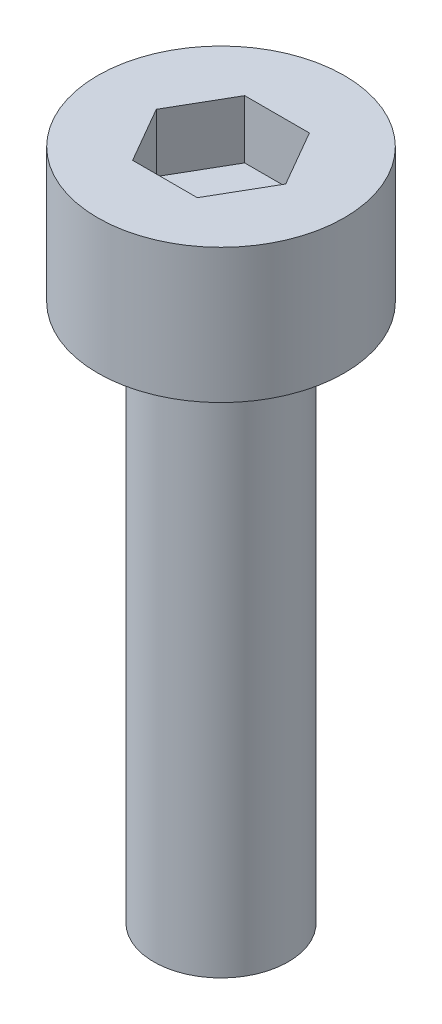
SolidWorks part; units mm, degrees
material "AISI 304"
ref_plane "前视基准面" through (0, 0, 0) normal (0, 0, 1) x (1, 0, 0)
ref_plane "上视基准面" through (0, 0, 0) normal (0, 1, 0) x (1, 0, 0)
ref_plane "右视基准面" through (0, 0, 0) normal (1, 0, 0) x (0, 0, -1)
sketch "草图1" plane through (0, 0, 0) normal (0, 1, 0) x (1, 0, 0)
  circle A0 centre (0, 0) radius 2.75
  dimension "D1" = 5.5
extrude "杯头" add sketch "草图1" along normal blind 3
sketch "草图2" plane through (0, 3, 0) normal (0, 1, 0) x (1, 0, 0)
  line L1 (1.4434, 0) -> (0.7217, 1.25)
  line L2 (0.7217, 1.25) -> (-0.7217, 1.25)
  line L3 (-0.7217, 1.25) -> (-1.4434, 0)
  line L4 (-1.4434, 0) -> (-0.7217, -1.25)
  line L5 (-0.7217, -1.25) -> (0.7217, -1.25)
  line L6 (0.7217, -1.25) -> (1.4434, 0)
  circle A0 centre (0, 0) radius 1.25 construction
  dimension "D1" = 2.5
extrude "内六角口" cut sketch "草图2" against normal blind 1.3
sketch "草图3" plane through (0, 0, 0) normal (0, -1, 0) x (1, 0, 0)
  circle A0 centre (0, 0) radius 1.5
  dimension "D1" = 3
extrude "螺纹长" add sketch "草图3" along normal blind 12
